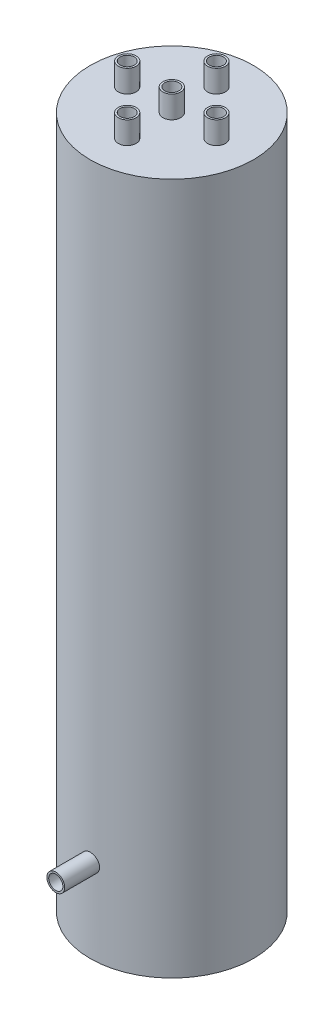
SolidWorks part; units mm, degrees
ref_plane "Front Plane" through (0, 0, 0) normal (0, 0, 1) x (1, 0, 0)
ref_plane "Top Plane" through (0, 0, 0) normal (0, 1, 0) x (1, 0, 0)
ref_plane "Right Plane" through (0, 0, 0) normal (1, 0, 0) x (0, 0, -1)
sketch "Sketch2" plane through (0, 0, 0) normal (0, 1, 0) x (1, 0, 0)
  circle A0 centre (0, 0) radius 29.45
  circle A1 centre (0, 0) radius 36.6
  dimension "D1" = 58.9
  dimension "D2" = 73.2
extrude "Boss-Extrude1" add sketch "Sketch2" along normal mid plane 280
sketch "Sketch3" plane through (0, 140, 0) normal (0, 1, 0) x (1, 0, 0)
  circle A0 centre (0, 0) radius 36.6
extrude "Boss-Extrude2" add sketch "Sketch3" along normal blind 15
sketch "Sketch5" plane through (0, 0, 0) normal (0, 0, 1) x (1, 0, 0)
  circle A0 centre (0, -117.7045) radius 3.175
  dimension "D1" = 6.35
extrude "Cut-Extrude1" cut sketch "Sketch5" along normal blind 52
sketch "Sketch6" plane through (0, 0, 0) normal (0, 0, 1) x (1, 0, 0)
  circle A0 centre (0, -117.7045) radius 3.175
  circle A1 centre (0, -117.7045) radius 4
  dimension "D1" = 6.35
  dimension "D2" = 8
extrude "Boss-Extrude4" add sketch "Sketch6" along normal blind 52
sketch "Sketch7" plane through (0, 155, 0) normal (0, 1, 0) x (1, 0, 0)
  circle A0 centre (0, 20) radius 3.175
  circle A1 centre (0, 0) radius 3.175
  circle A2 centre (-20, 0) radius 3.175
  circle A3 centre (20, 0) radius 3.175
  circle A4 centre (0, -20) radius 3.175
  dimension "D1" = 6.35
  dimension "D2" = 6.35
  dimension "D3" = 6.35
  dimension "D4" = 6.35
  dimension "D5" = 6.35
  dimension "D6" = 20
  dimension "D7" = 20
  dimension "D8" = 20
  dimension "D9" = 20
extrude "Cut-Extrude2" cut sketch "Sketch7" against normal blind 52
sketch "Sketch8" plane through (0, 155, 0) normal (0, 1, 0) x (1, 0, 0)
  circle A0 centre (0, 0) radius 3.175
  circle A1 centre (20, 0) radius 3.175
  circle A2 centre (0, 20) radius 3.175
  circle A3 centre (-20, 0) radius 3.175
  circle A4 centre (0, -20) radius 3.175
  circle A5 centre (0, 0) radius 4
  circle A6 centre (0, 20) radius 4
  circle A7 centre (20, 0) radius 4
  circle A8 centre (-20, 0) radius 4
  circle A9 centre (0, -20) radius 4
  dimension "D1" = 6.35
  dimension "D2" = 8
  dimension "D3" = 6.35
  dimension "D4" = 8
  dimension "D5" = 6.35
  dimension "D6" = 8
  dimension "D7" = 6.35
  dimension "D8" = 8
  dimension "D9" = 6.35
  dimension "D10" = 8
extrude "Boss-Extrude5" add sketch "Sketch8" along normal blind 10
sketch "Sketch4" plane through (0, -140, 0) normal (0, -1, 0) x (1, 0, 0)
  circle A0 centre (0, 0) radius 36.6
extrude "Boss-Extrude3" add sketch "Sketch4" along normal blind 15
